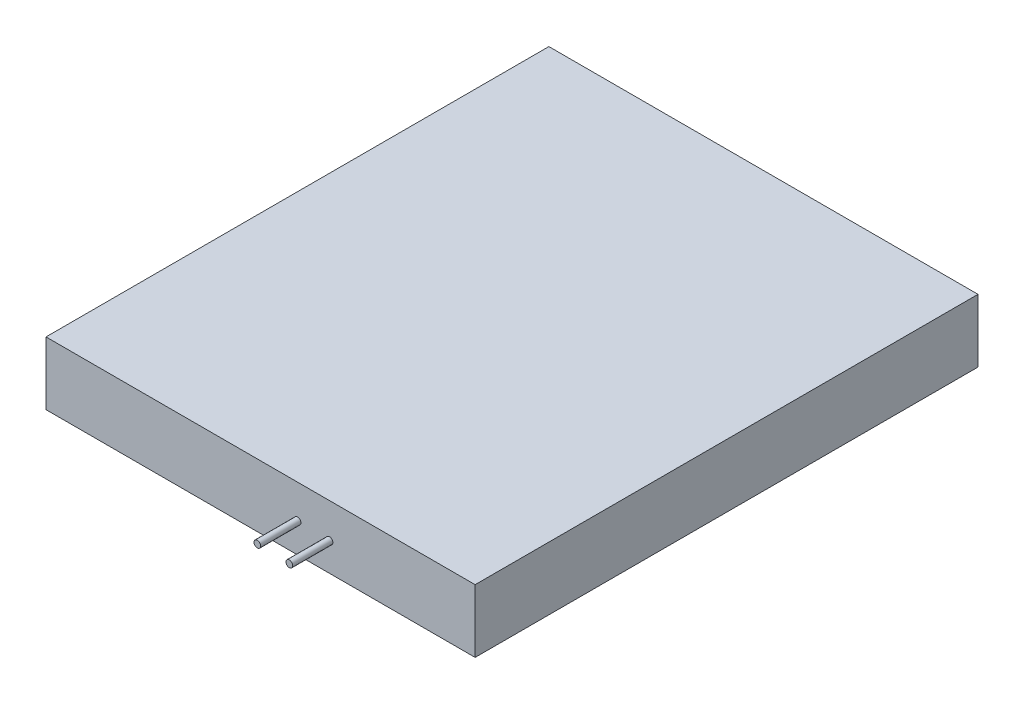
SolidWorks part; units mm, degrees
ref_plane "Front Plane" through (0, 0, 0) normal (0, 0, 1) x (1, 0, 0)
ref_plane "Top Plane" through (0, 0, 0) normal (0, 1, 0) x (1, 0, 0)
ref_plane "Right Plane" through (0, 0, 0) normal (1, 0, 0) x (0, 0, -1)
sketch "Sketch1" plane through (0, 0, 0) normal (0, 1, 0) x (1, 0, 0)
  line L1 (0, 0) -> (64, 0)
  line L2 (0, 0) -> (0, 75)
  line L3 (0, 75) -> (64, 75)
  line L4 (64, 0) -> (64, 75)
extrude "Boss-Extrude1" add sketch "Sketch1" along normal blind 9.4
sketch "Sketch3" plane through (13.5259, 0, 0) normal (0, 0, 1) x (1, 0, 0)
  circle A0 centre (23.99, 4.3972) radius 0.5
  circle A1 centre (28.7594, 4.2341) radius 0.5
extrude "Boss-Extrude2" add sketch "Sketch3" along normal blind 6
